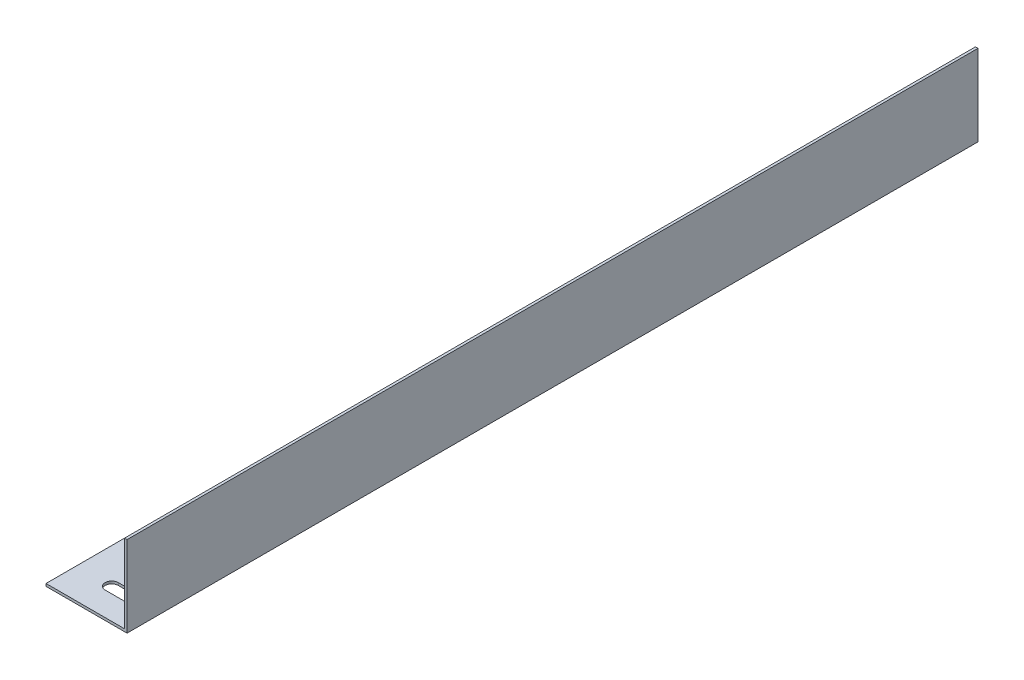
SolidWorks part; units mm, degrees
ref_plane "Front Plane" through (0, 0, 0) normal (0, 0, 1) x (1, 0, 0)
ref_plane "Top Plane" through (0, 0, 0) normal (0, 1, 0) x (1, 0, 0)
ref_plane "Right Plane" through (0, 0, 0) normal (1, 0, 0) x (0, 0, -1)
sketch "Sketch1" plane through (0, 0, 0) normal (0, 0, 1) x (1, 0, 0)
  line L0 (0, 0) -> (50.8, 0)
  line L1 (50.8, 0) -> (50.8, 50.8)
  line L2 (50.8, 50.8) -> (49.2125, 50.8)
  line L3 (49.2125, 50.8) -> (49.2125, 1.5875)
  line L4 (49.2125, 1.5875) -> (0, 1.5875)
  line L5 (0, 1.5875) -> (0, 0)
  dimension "D1" = 50.8
  dimension "D2" = 50.8
  dimension "D3" = 1.5875
  dimension "D4" = 1.5875
extrude "Extrude1" add sketch "Sketch1" along normal blind 533.4
sketch "Sketch2" plane through (0, 0, 0) normal (0, -1, 0) x (1, 0, 0)
  line L0 (22.1615, 514.35) -> (-21.2101, 514.35) construction
  line L1 (0, 533.4) -> (50.8, 533.4) construction
  line L2 (22.1615, 514.35) -> (61.6491, 514.35) construction
  line L3 (0, 266.7) -> (50.8, 266.7) construction
  line L4 (0, 533.4) -> (0, 0) construction
  line L5 (50.8, 533.4) -> (50.8, 0) construction
  line L6 (22.1615, 518.4521) -> (34.8615, 518.4521)
  line L7 (22.1615, 510.2479) -> (34.8615, 510.2479)
  arc A0 (34.8615, 510.2479) -> (34.8615, 518.4521) centre (34.8615, 514.35) ccw
  circle A1 centre (22.1615, 57.15) radius 4.1021
  circle A2 centre (22.1615, 476.25) radius 4.1021
  circle A3 centre (22.1615, 19.05) radius 4.1021
  arc A4 (22.1615, 518.4521) -> (22.1615, 510.2479) centre (22.1615, 514.35) ccw
  dimension "D1" = 8.2042
  dimension "D4" = 8.2042
  dimension "D6" = 12.7
  dimension "D2" = 19.05
  dimension "D3" = 28.6385
  dimension "D5" = 38.1
  dimension "D8" = 28.6385
extrude "Cut-Extrude1" cut sketch "Sketch2" against normal through all
